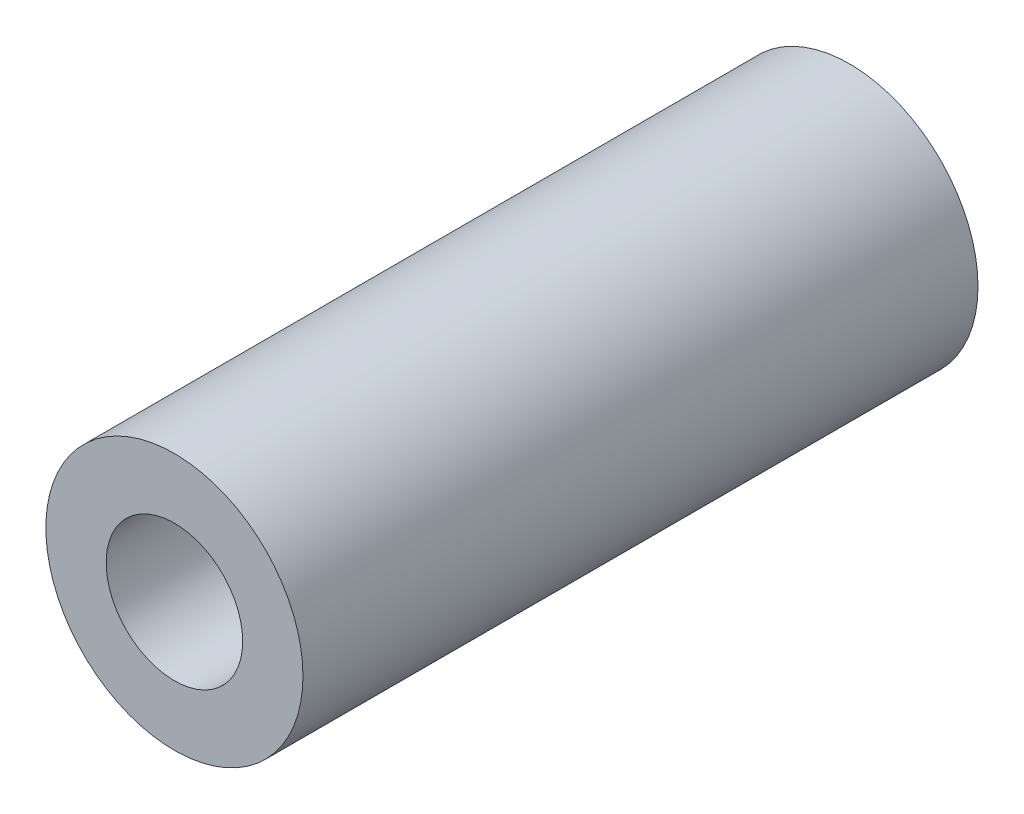
SolidWorks part; units mm, degrees
ref_plane "Plan de face" through (0, 0, 0) normal (0, 0, 1) x (1, 0, 0)
ref_plane "Plan de dessus" through (0, 0, 0) normal (0, 1, 0) x (1, 0, 0)
ref_plane "Plan de droite" through (0, 0, 0) normal (1, 0, 0) x (0, 0, -1)
sketch "Esquisse1" plane through (0, 0, 0) normal (0, 0, 1) x (1, 0, 0)
  circle A0 centre (0, 0) radius 9
  circle A1 centre (0, 0) radius 16.95
  dimension "D1" = 18
  dimension "D2" = 33.9
extrude "Boss.-Extru.1" add sketch "Esquisse1" along normal blind 89
